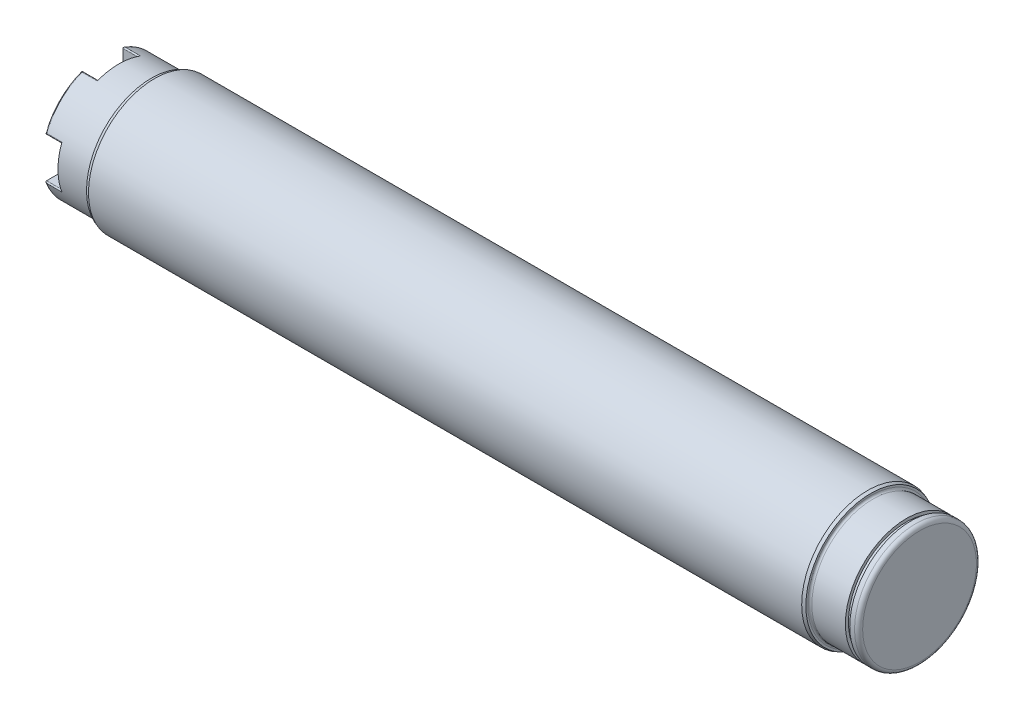
SolidWorks part; units mm, degrees
ref_plane "Front" through (0, 0, 0) normal (0, 0, 1) x (1, 0, 0)
ref_plane "Top" through (0, 0, 0) normal (0, 1, 0) x (1, 0, 0)
ref_plane "Right" through (0, 0, 0) normal (1, 0, 0) x (0, 0, -1)
sketch "Sketch1" plane through (0, 0, 0) normal (0, 0, 1) x (1, 0, 0)
  line L0 (-283, 0) -> (11.2597, 0) construction
  line L1 (-201, 20) -> (-201, 30)
  line L2 (-201, 20) -> (-193, 20)
  line L3 (-193, 20) -> (-193, 8.5)
  line L4 (-201, 30) -> (-177, 30)
  line L5 (0, -32.8854) -> (0, 65.4134) construction
  line L6 (194.5, 30) -> (194.5, 28.5)
  line L7 (194.5, 28.5) -> (196.65, 28.5)
  line L8 (201, 0) -> (201, 28)
  line L9 (-146.794, 0) -> (201, 0)
  line L10 (-177, 30) -> (-177, 31.954)
  line L11 (-175.5, 32.5) -> (175.5, 32.5)
  line L12 (177, 30) -> (194.5, 30)
  line L13 (-177, 31.954) -> (-175.5, 32.5)
  line L14 (177, 31.954) -> (175.5, 32.5)
  line L15 (177, 30) -> (177, 31.954)
  line L16 (-193, 8.5) -> (-183, 8.5)
  line L17 (-183, 8.5) -> (-182.0987, 7)
  line L18 (-182.0987, 7) -> (-151, 7)
  line L19 (-151, 7) -> (-146.794, 0)
  line L20 (196.65, 28.5) -> (196.65, 30)
  line L21 (196.65, 30) -> (199, 30)
  arc A0 (201, 28) -> (199, 30) centre (199, 28) ccw
  point P21 (0, 32.5)
  point P27 (201, 30)
  dimension "D18" = 2
  dimension "D1" = 402
  dimension "D2" = 24
  dimension "D3" = 8
  dimension "D4" = 40
  dimension "D5" = 60
  dimension "D6" = 65
  dimension "D7" = 17
  dimension "D8" = 20
  dimension "D9" = 1.5
  dimension "D10" = 14
  dimension "D11" = 59
  dimension "D12" = 59
  dimension "D13" = 10
  dimension "D14" = 42
  dimension "D15" = 6.5
  dimension "D16" = 2.15
  dimension "D17" = 57
  dimension "D19" = 354
  dimension "D20" = 17.5
  dimension "D21" = 201
revolve "Base-Revolve" add sketch "Sketch1" angle 360 about L0
cosmetic thread "Cosmetic Thread2" parameters "D1"=24.1, "D2"=16
fillet "R1 runding" radius 1 2 edges at (177, 0, 30) (-177, 0, 30)
sketch "Sketch3" plane through (-201, 0, 0) normal (-1, 0, 0) x (0, 0, 1)
  line L0 (0, 0) -> (30, 0) construction
  line L1 (0, 0) -> (0, 30) construction
  line L2 (10, 28.2843) -> (10, 17.3205)
  line L3 (-10, 28.2843) -> (-10, 17.3205)
  line L4 (17.3205, 10) -> (28.2843, 10)
  line L5 (17.3205, -10) -> (28.2843, -10)
  line L6 (-17.3205, -10) -> (-28.2843, -10)
  line L7 (-17.3205, 10) -> (-28.2843, 10)
  line L8 (-10, -28.2843) -> (-10, -17.3205)
  line L9 (10, -28.2843) -> (10, -17.3205)
  circle A0 centre (0, 0) radius 20 construction
  circle A1 centre (0, 0) radius 30 construction
  arc A2 (17.3205, -10) -> (17.3205, 10) centre (0, 0) ccw
  arc A3 (28.2843, -10) -> (28.2843, 10) centre (0, 0) ccw
  arc A4 (-10, -17.3205) -> (10, -17.3205) centre (0, 0) ccw
  arc A5 (-10, -28.2843) -> (10, -28.2843) centre (0, 0) ccw
  arc A6 (-28.2843, 10) -> (-28.2843, -10) centre (0, 0) ccw
  arc A7 (-17.3205, 10) -> (-17.3205, -10) centre (0, 0) ccw
  arc A8 (10, 17.3205) -> (-10, 17.3205) centre (0, 0) ccw
  arc A9 (10, 28.2843) -> (-10, 28.2843) centre (0, 0) ccw
  dimension "D1" = 20
  dimension "D2" = 20
extrude "Affræsning" cut sketch "Sketch3" against normal blind 8
fillet "R0.5 rundinger" radius 0.5 20 edges at (-197, -10, 17.3205) (-197, -17.3205, 10) (-197, 10, -28.2843) (-197, 10, 17.3205) (-197, 17.3205, 10) (-197, -10, -28.2843) (-197, -10, -17.3205) (-197, -17.3205, -10) (-197, -28.2843, -10) (-197, -28.2843, 10) (-197, -10, 28.2843) (-197, 28.2843, 10) (-197, 10, 28.2843) (-197, 10, -17.3205) (-197, 28.2843, -10) (-197, 17.3205, -10) (-201, 21.2132, -21.2132) (-201, 21.2132, 21.2132) (-201, -21.2132, 21.2132) (-201, -21.2132, -21.2132)
